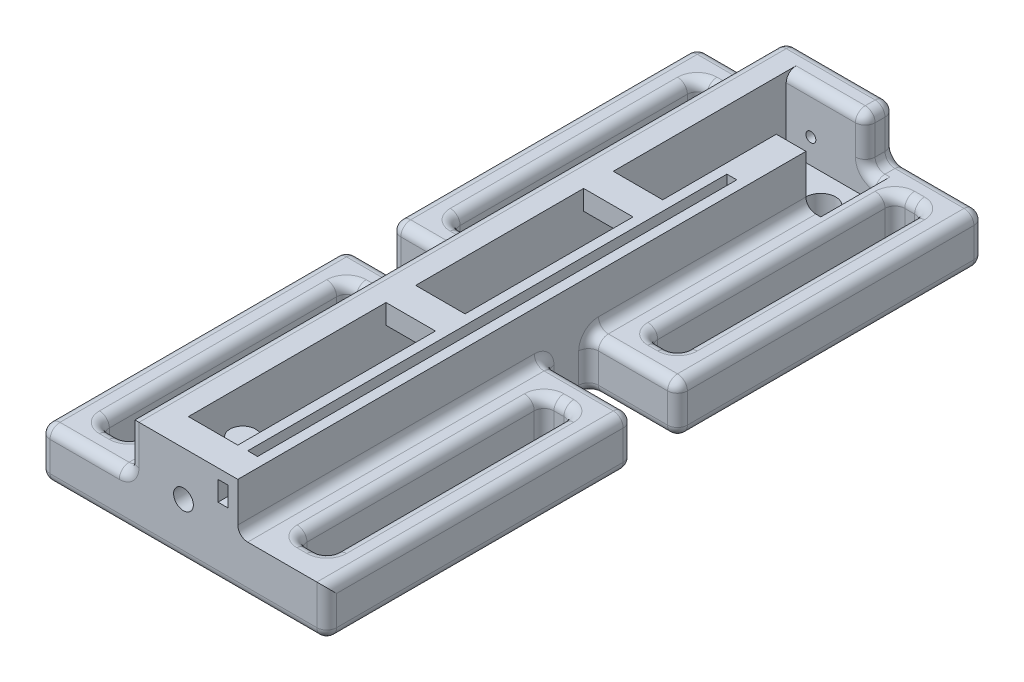
SolidWorks part; units mm, degrees
ref_plane "Front Plane" through (0, 0, 0) normal (0, 0, 1) x (1, 0, 0)
ref_plane "Top Plane" through (0, 0, 0) normal (0, 1, 0) x (1, 0, 0)
ref_plane "Right Plane" through (0, 0, 0) normal (1, 0, 0) x (0, 0, -1)
sketch "Sketch1" plane through (0, 0, 0) normal (0, 1, 0) x (1, 0, 0)
  line L1 (0, 0) -> (11, 0)
  line L2 (0, 0) -> (0, 66.5)
  line L3 (0, 66.5) -> (11, 66.5)
  line L4 (11, 0) -> (11, 66.5)
extrude "Boss-Extrude2" add sketch "Sketch1" along normal blind 10 contours L3 L4 L1 L2
sketch "Sketch2" plane through (0, 10, 0) normal (0, 1, 0) x (1, 0, 0)
  line L0 (8, 63.5) -> (8, 3)
  line L1 (3, 3) -> (8, 3)
  line L2 (3, 3) -> (3, 63.5)
  line L3 (3, 63.5) -> (8, 63.5)
  line L4 (0, 66.5) -> (11, 66.5) construction
  line L12 (0, 0) -> (0, 66.5) construction
  line L14 (0, 0) -> (11, 0) construction
  dimension "D2" = 3
  dimension "D5" = 5
  dimension "D10" = 3
  dimension "D11" = 3
extrude "Cut-Extrude1" cut sketch "Sketch2" against normal blind 7
sketch "Sketch3" plane through (0, 0, 0) normal (0, 1, 0) x (1, 0, 0)
  line L0 (0, 0) -> (0, 66.5) construction
  line L1 (0, 0) -> (-9, 0)
  line L2 (0, 0) -> (0, 31)
  line L3 (0, 31) -> (-9, 31)
  line L4 (-9, 0) -> (-9, 31)
  line L5 (11, 0) -> (20, 0)
  line L6 (11, 0) -> (11, 31)
  line L7 (11, 31) -> (20, 31)
  line L8 (20, 0) -> (20, 31)
  line L17 (0, 66.5) -> (-9, 66.5)
  line L18 (0, 66.5) -> (0, 35.5)
  line L19 (0, 35.5) -> (-9, 35.5)
  line L20 (-9, 66.5) -> (-9, 35.5)
  line L21 (11, 0) -> (11, 66.5) construction
  line L22 (11, 66.5) -> (20, 66.5)
  line L23 (11, 66.5) -> (11, 35.5)
  line L24 (11, 35.5) -> (20, 35.5)
  line L25 (20, 66.5) -> (20, 35.5)
  line L27 (-6, 28) -> (-3, 28)
  line L28 (-6, 28) -> (-6, 3)
  line L29 (-6, 3) -> (-3, 3)
  line L30 (-3, 28) -> (-3, 3)
  line L31 (14, 28) -> (17, 28)
  line L32 (14, 28) -> (14, 3)
  line L33 (14, 3) -> (17, 3)
  line L34 (17, 28) -> (17, 3)
  line L39 (14, 63.5) -> (17, 63.5)
  line L40 (14, 63.5) -> (14, 38.5)
  line L41 (14, 38.5) -> (17, 38.5)
  line L42 (17, 63.5) -> (17, 38.5)
  line L43 (-6, 63.5) -> (-3, 63.5)
  line L44 (-6, 63.5) -> (-6, 38.5)
  line L45 (-6, 38.5) -> (-3, 38.5)
  line L46 (-3, 63.5) -> (-3, 38.5)
  dimension "D13" = 3
  dimension "D14" = 3
  dimension "D15" = 25
  dimension "D16" = 3
  dimension "D17" = 3
  dimension "D18" = 3
  dimension "D19" = 3
  dimension "D20" = 3
  dimension "D21" = 3
  dimension "D22" = 3
  dimension "D23" = 25
  dimension "D24" = 3
  dimension "D25" = 25
  dimension "D26" = 3
  dimension "D27" = 3
  dimension "D28" = 3
  dimension "D29" = 3
  dimension "D30" = 3
  dimension "D31" = 3
  dimension "D32" = 3
  dimension "D33" = 3
  dimension "D34" = 3
  dimension "D35" = 3
  dimension "D36" = 25
  dimension "D40" = 4.5
extrude "Boss-Extrude3" add sketch "Sketch3" along normal blind 5
sketch "Sketch4" plane through (0, 3, 0) normal (0, 1, 0) x (1, 0, 0)
  line L1 (8, 63.5) -> (8, 3) construction
  line L3 (3, 3) -> (8, 3) construction
  circle A0 centre (5.5, 6) radius 1.3
  dimension "D2" = 2.5
  dimension "D4" = 3
extrude "Boss-Extrude4" add sketch "Sketch4" along normal blind 5
sketch "Sketch5" plane through (0, 10, 0) normal (0, 1, 0) x (1, 0, 0)
  line L0 (3, 3) -> (3, 63.5) construction
  line L1 (3, 23) -> (8, 23)
  line L2 (3, 23) -> (3, 26)
  line L3 (3, 26) -> (8, 26)
  line L4 (8, 23) -> (8, 26)
  line L6 (8, 63.5) -> (8, 3) construction
  line L7 (3, 43) -> (8, 43)
  line L8 (3, 43) -> (3, 46)
  line L9 (3, 46) -> (8, 46)
  line L10 (8, 43) -> (8, 46)
  circle A0 centre (5.5, 6) radius 1.3 construction
  dimension "D1" = 17
  dimension "D2" = 3
  dimension "D3" = 37
  dimension "D4" = 3
extrude "Boss-Extrude5" add sketch "Sketch5" against normal blind 2
sketch "Sketch6" plane through (0, 10, 0) normal (0, 1, 0) x (1, 0, 0)
  line L0 (8, 46) -> (3, 46) construction
  line L1 (11, 0) -> (11, 66.5) construction
  circle A0 centre (9.5, 60.5) radius 1.51
  dimension "D1" = 14.5
  dimension "D2" = 1.5
extrude "Cut-Extrude4" cut sketch "Sketch6" against normal blind 10
sketch "Sketch7" plane through (0, 10, 0) normal (0, 1, 0) x (1, 0, 0)
  line L0 (8, 63.5) -> (8, 60.6735) construction
  line L1 (8, 63.5) -> (12.5, 63.5)
  line L2 (8, 63.5) -> (8, 57.5)
  line L3 (8, 57.5) -> (12.5, 57.5)
  line L4 (12.5, 63.5) -> (12.5, 57.5)
  arc A0 (11, 60.6735) -> (8, 60.6735) centre (9.5, 60.5) ccw construction
  arc A1 (8, 60.3265) -> (11, 60.3265) centre (9.5, 60.5) ccw construction
  arc A2 (11, 60.6735) -> (8, 60.6735) centre (9.5, 60.5) ccw construction
  dimension "D1" = 3
  dimension "D2" = 3
  dimension "D3" = 3
extrude "Cut-Extrude5" cut sketch "Sketch7" against normal blind 7
sketch "Sketch10" plane through (0, 0, -66.5) normal (0, 0, 1) x (1, 0, 0)
  line L2 (3, 3) -> (3, 10) construction
  line L6 (3, 3) -> (12.5, 3) construction
  circle A0 centre (5.5, 5.5) radius 0.5
  dimension "D2" = 2.5
  dimension "D4" = 2.5
extrude "Cut-Extrude6" cut sketch "Sketch10" along normal blind 3
sketch "Sketch11" plane through (0, 0, -3) normal (0, 0, -1) x (-1, 0, 0)
  line L6 (-3, 3) -> (-8, 3) construction
  line L7 (-8, 3) -> (-8, 10) construction
  circle A3 centre (-5.5, 5.5) radius 1
  dimension "D7" = 2.5
  dimension "D8" = 2.5
extrude "Cut-Extrude7" cut sketch "Sketch11" against normal blind 3
sketch "Sketch12" plane through (0, 10, 0) normal (0, 1, 0) x (1, 0, 0)
  line L5 (0, 0) -> (11, 0) construction
  line L6 (8, 57.5) -> (11, 57.5) construction
  line L7 (9, 0) -> (10, 0)
  line L8 (9, 0) -> (9, 57.5)
  line L9 (9, 57.5) -> (10, 57.5)
  line L10 (10, 0) -> (10, 57.5)
  line L14 (8, 57.5) -> (8, 46) construction
  line L44 (9, 0) -> (10, 0)
  line L45 (9, 0) -> (9, 3)
  line L46 (9, 3) -> (10, 3)
  line L47 (10, 0) -> (10, 3)
  line L49 (10, 14.5) -> (10, 11.5)
  line L51 (9, 14.5) -> (9, 11.5)
  line L53 (10, 26) -> (10, 23)
  line L55 (9, 26) -> (9, 23)
  line L57 (10, 36.4083) -> (10, 33.4371)
  line L59 (9, 36.4083) -> (9, 33.4371)
  line L61 (10, 46) -> (10, 43)
  line L63 (9, 46) -> (9, 43)
  line L65 (10, 55.5) -> (10, 52.5)
  line L67 (9, 55.5) -> (9, 52.5)
  line L68 (10, 54.5) -> (9, 54.5)
  line L69 (10, 54.5) -> (10, 51.5)
  line L70 (10, 51.5) -> (9, 51.5)
  line L71 (9, 54.5) -> (9, 51.5)
  line L79 (3, 3) -> (8, 3) construction
  dimension "D4" = 1
  dimension "D12" = 0
  dimension "D24" = 3
  dimension "D25" = 3
extrude "Cut-Extrude8" cut sketch "Sketch12" against normal blind 3
sketch "Sketch13" plane through (0, 0, -57.5) normal (0, 0, -1) x (-1, 0, 0)
  line L6 (-10, 9) -> (-9, 9)
  line L7 (-10, 9) -> (-10, 7)
  line L8 (-10, 7) -> (-9, 7)
  line L9 (-9, 9) -> (-9, 7)
extrude "Cut-Extrude9" cut sketch "Sketch13" against normal blind 68
fillet "Fillet1" radius 1 97 edges at (15.5, 5, -66.5) (15.5, 5, -38.5) (15.5, 0, -38.5) (15.5, 5, -63.5) (15.5, 0, -63.5) (-4.5, 0, -38.5) (-4.5, 5, -38.5) (-4.5, 0, -63.5) (-4.5, 5, -63.5) (-4.5, 0, -28) (-4.5, 5, -28) (-4.5, 0, -3) (-4.5, 5, -3) (-4.5, 0, -35.5) (-4.5, 5, -35.5) (11, 5, -46.5) (15.5, 5, -28) (15.5, 0, -28) (15.5, 5, -3) (15.5, 0, -3) (11, 7.5, -66.5) (11, 5, -65) (11, 7.5, -63.5) (11, 10, -65) (14, 2.5, -3) (14, 5, -15.5) (14, 2.5, -28) (14, 0, -15.5) (17, 2.5, -63.5) (17, 5, -51) (17, 2.5, -38.5) (17, 0, -51) (14, 2.5, -38.5) (14, 5, -51) (14, 2.5, -63.5) (14, 0, -51) (-3, 2.5, -63.5) (-3, 2.5, -38.5) (-3, 0, -51) (-3, 5, -51) (-6, 2.5, -38.5) (-6, 2.5, -63.5) (-6, 0, -51) (-6, 5, -51) (-6, 2.5, -3) (-6, 2.5, -28) (-6, 0, -15.5) (-6, 5, -15.5) (-3, 2.5, -28) (-3, 2.5, -3) (-3, 0, -15.5) (-3, 5, -15.5) (0, 10, -33.25) (0, 2.5, -35.5) (0, 7.5, -66.5) (15.5, 5, -31) (11, 2.5, -35.5) (15.5, 5, -35.5) (15.5, 0, -35.5) (20, 2.5, 0) (20, 5, -15.5) (20, 2.5, -31) (20, 0, -15.5) (17, 2.5, -28) (17, 5, -15.5) (17, 2.5, -3) (17, 0, -15.5) (20, 2.5, -35.5) (20, 5, -51) (20, 2.5, -66.5) (20, 0, -51) (-4.5, 5, -31) (-4.5, 5, -66.5) (0, 5, -51) (-9, 2.5, -66.5) (-9, 5, -51) (-9, 2.5, -35.5) (-9, 0, -51) (-9, 2.5, -31) (-9, 5, -15.5) (-9, 2.5, 0) (-9, 0, -15.5) (11.75, 5, -63.5) (5.5, 0, 0) (5.5, 0, -66.5) (5.5, 10, -66.5) (7, 10, -63.5)
